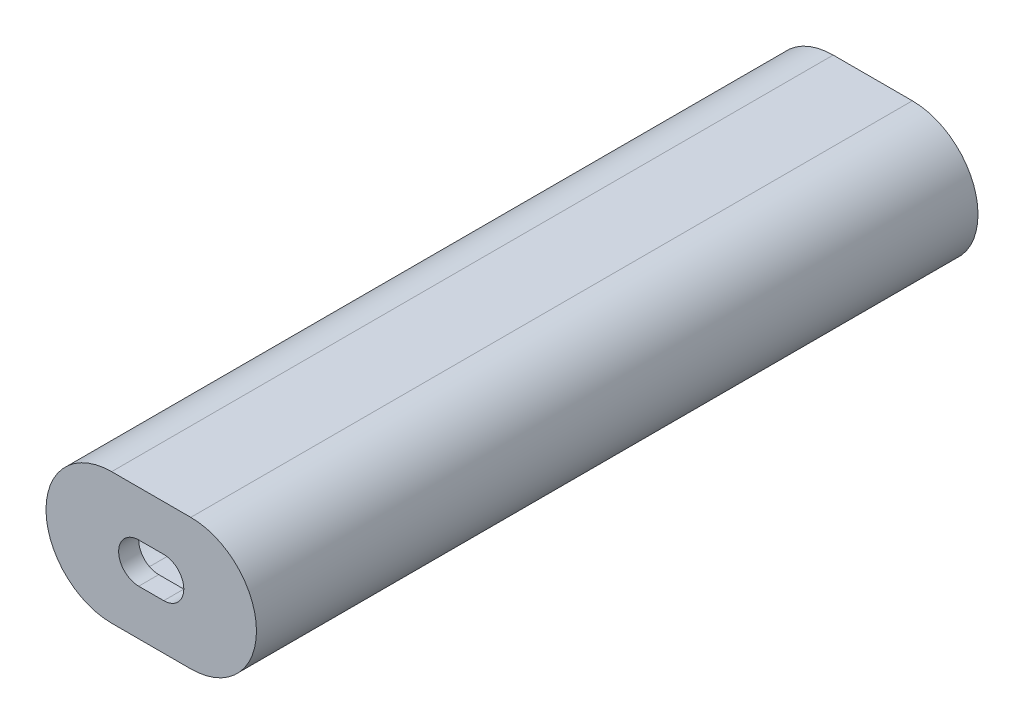
SolidWorks part; units mm, degrees
ref_plane "Front Plane" through (0, 0, 0) normal (0, 0, 1) x (1, 0, 0)
ref_plane "Top Plane" through (0, 0, 0) normal (0, 1, 0) x (1, 0, 0)
ref_plane "Right Plane" through (0, 0, 0) normal (1, 0, 0) x (0, 0, -1)
sketch "Sketch1" plane through (0, 0, 0) normal (0, 0, 1) x (1, 0, 0)
  line L0 (-12.573, 0) -> (12.573, 0) construction
  line L1 (-12.573, 11.557) -> (12.573, 11.557)
  line L2 (-12.573, -11.557) -> (12.573, -11.557)
  line L3 (-10.033, 0) -> (10.033, 0) construction
  line L4 (-10.033, 16.637) -> (10.033, 16.637)
  line L5 (-10.033, -16.637) -> (10.033, -16.637)
  line L6 (-24.13, 0) -> (-26.67, 0)
  line L7 (24.13, 0) -> (26.67, 0)
  arc A0 (-12.573, 11.557) -> (-12.573, -11.557) centre (-12.573, 0) ccw
  arc A1 (12.573, -11.557) -> (12.573, 11.557) centre (12.573, 0) ccw
  arc A2 (-10.033, 16.637) -> (-10.033, -16.637) centre (-10.033, 0) ccw
  arc A3 (10.033, -16.637) -> (10.033, 16.637) centre (10.033, 0) ccw
  point P2 (0, 0)
  point P8 (-24.13, 0)
  point P9 (24.13, 0)
  point P12 (0, 0)
  point P17 (-26.67, 0)
  dimension "D2" = 23.114
  dimension "D4" = 2.54
  dimension "D1" = 48.26
  dimension "D3" = 5.08
extrude "Boss-Extrude1" add sketch "Sketch1" against normal blind 177.8 contours L7 A3 L4 A2 L6 A0 L1 A1 | L5 A3 L7 A1 L2 A0 L6 A2
sketch "Sketch3" plane through (0, 0, 0) normal (0, 0, 1) x (1, 0, 0)
  line L0 (-10.033, 0) -> (10.033, 0) construction
  line L1 (-10.033, 16.637) -> (10.033, 16.637)
  line L2 (-10.033, -16.637) -> (10.033, -16.637)
  line L3 (-10.033, 16.637) -> (10.033, 16.637) construction
  arc A0 (-10.033, 16.637) -> (-10.033, -16.637) centre (-10.033, 0) ccw
  arc A1 (10.033, -16.637) -> (10.033, 16.637) centre (10.033, 0) ccw
  arc A2 (-10.033, 16.637) -> (-10.033, -16.637) centre (-10.033, 0) ccw construction
  point P2 (0, 0)
  point P8 (-26.67, 0)
  point P9 (-26.67, 0)
  dimension "D1" = 0
extrude "Boss-Extrude2" add sketch "Sketch3" along normal blind 5.08
sketch "Sketch4" plane through (0, 0, 0) normal (0, 0, 1) x (1, 0, 0)
  line L1 (-30.7622, 14.8905) -> (26.67, 14.8905)
  line L2 (-30.7622, 14.8905) -> (-30.7622, 0)
  line L3 (-30.7622, 0) -> (26.67, 0)
  line L4 (26.67, 14.8905) -> (26.67, 0)
  arc A0 (10.033, -16.637) -> (10.033, 16.637) centre (10.033, 0) ccw construction
sketch "Sketch5" plane through (0, -11.557, 0) normal (0, 1, 0) x (1, 0, 0)
  line L2 (-10.033, -5.08) -> (10.033, -5.08) construction
  line L3 (-10.033, 177.8) -> (10.033, 177.8) construction
  circle A0 centre (0, 119.888) radius 3.683
  circle A1 centre (0, 52.832) radius 3.683
  dimension "D1" = 7.366
  dimension "D3" = 7.366
  dimension "D2" = 57.912
  dimension "D4" = 57.912
extrude "Cut-Extrude2" cut sketch "Sketch5" against normal blind 4.191
sketch "Sketch6" plane through (0, -11.557, 0) normal (0, 1, 0) x (1, 0, 0)
  line L0 (-10.033, -5.08) -> (10.033, -5.08) construction
  line L1 (-10.033, 177.8) -> (10.033, 177.8) construction
  circle A0 centre (0, 119.888) radius 2.286
  circle A1 centre (0, 52.832) radius 2.286
  point P6 (0, 177.8)
  dimension "D3" = 4.572
  dimension "D4" = 4.572
  dimension "D1" = 57.912
  dimension "D2" = 57.912
extrude "Cut-Extrude3" cut sketch "Sketch6" against normal blind 6.731
sketch "Sketch7" plane through (0, 0, 5.08) normal (0, 0, 1) x (1, 0, 0)
  line L0 (-3.175, 0) -> (3.175, 0) construction
  line L1 (-3.175, 5.08) -> (3.175, 5.08)
  line L2 (-3.175, -5.08) -> (3.175, -5.08)
  arc A0 (-3.175, 5.08) -> (-3.175, -5.08) centre (-3.175, 0) ccw
  arc A1 (3.175, -5.08) -> (3.175, 5.08) centre (3.175, 0) ccw
  point P2 (0, 0)
  dimension "D2" = 5.08
  dimension "D1" = 6.35
  dimension "D3" = 0
extrude "Cut-Extrude5" cut sketch "Sketch7" against normal blind 5.08
